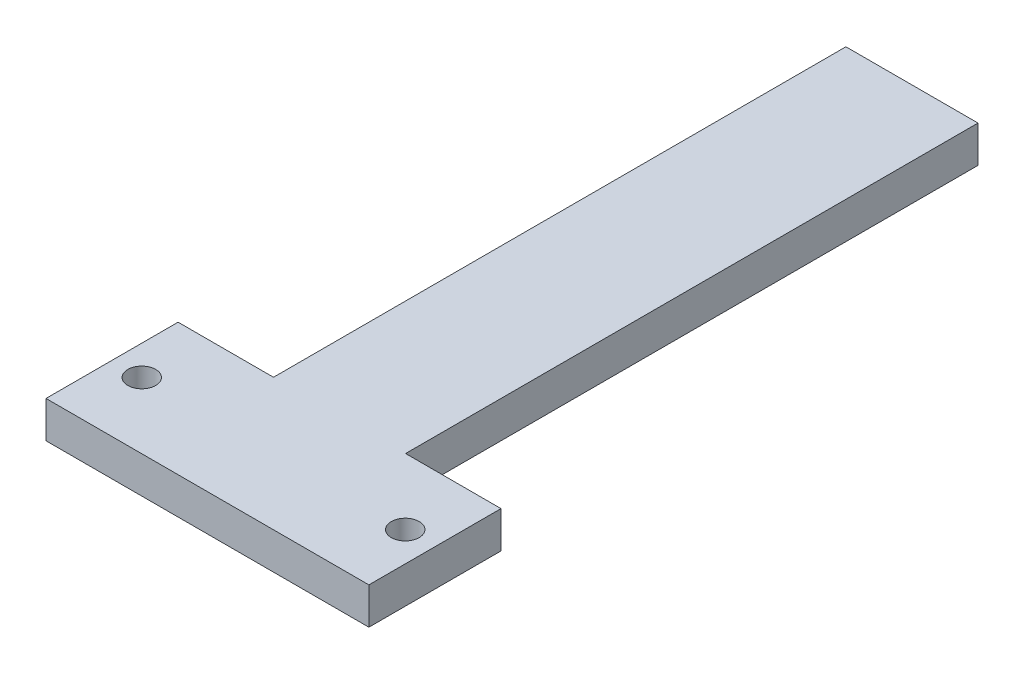
SolidWorks part; units mm, degrees
ref_plane "Front Plane" through (0, 0, 0) normal (0, 0, 1) x (1, 0, 0)
ref_plane "Top Plane" through (0, 0, 0) normal (0, 1, 0) x (1, 0, 0)
ref_plane "Right Plane" through (0, 0, 0) normal (1, 0, 0) x (0, 0, -1)
sketch "Sketch1" plane through (0, 0, 0) normal (0, 1, 0) x (1, 0, 0)
  line L1 (27.94, -11.43) -> (-27.94, -11.43)
  line L2 (27.94, -11.43) -> (27.94, 11.43)
  line L3 (27.94, 11.43) -> (-27.94, 11.43)
  line L4 (-27.94, -11.43) -> (-27.94, 11.43)
  line L5 (27.94, -11.43) -> (-27.94, 11.43) construction
  line L6 (27.94, 11.43) -> (-27.94, -11.43) construction
  line L7 (0, 11.43) -> (-11.43, 11.43)
  line L8 (0, 11.43) -> (0, 110.49)
  line L9 (0, 110.49) -> (-11.43, 110.49)
  line L10 (-11.43, 11.43) -> (-11.43, 110.49)
  line L11 (0, 11.43) -> (11.43, 11.43)
  line L12 (0, 11.43) -> (0, 110.49)
  line L13 (0, 110.49) -> (11.43, 110.49)
  line L14 (11.43, 11.43) -> (11.43, 110.49)
  circle A0 centre (-22.7965, 0) radius 2.413
  circle A1 centre (22.7965, 0) radius 2.413
  point P0 (0, 0)
  dimension "D6" = 4.826
  dimension "D7" = 4.826
  dimension "D8" = 45.593
  dimension "D9" = 22.7965
  dimension "D1" = 22.86
  dimension "D2" = 55.88
  dimension "D3" = 11.43
  dimension "D4" = 11.43
  dimension "D5" = 99.06
extrude "Boss-Extrude1" add sketch "Sketch1" along normal blind 6.35 contours L3 L14 L13 L8 | L10 L3 L8 L9 | L4 L1 L2 L3 A1 A0
